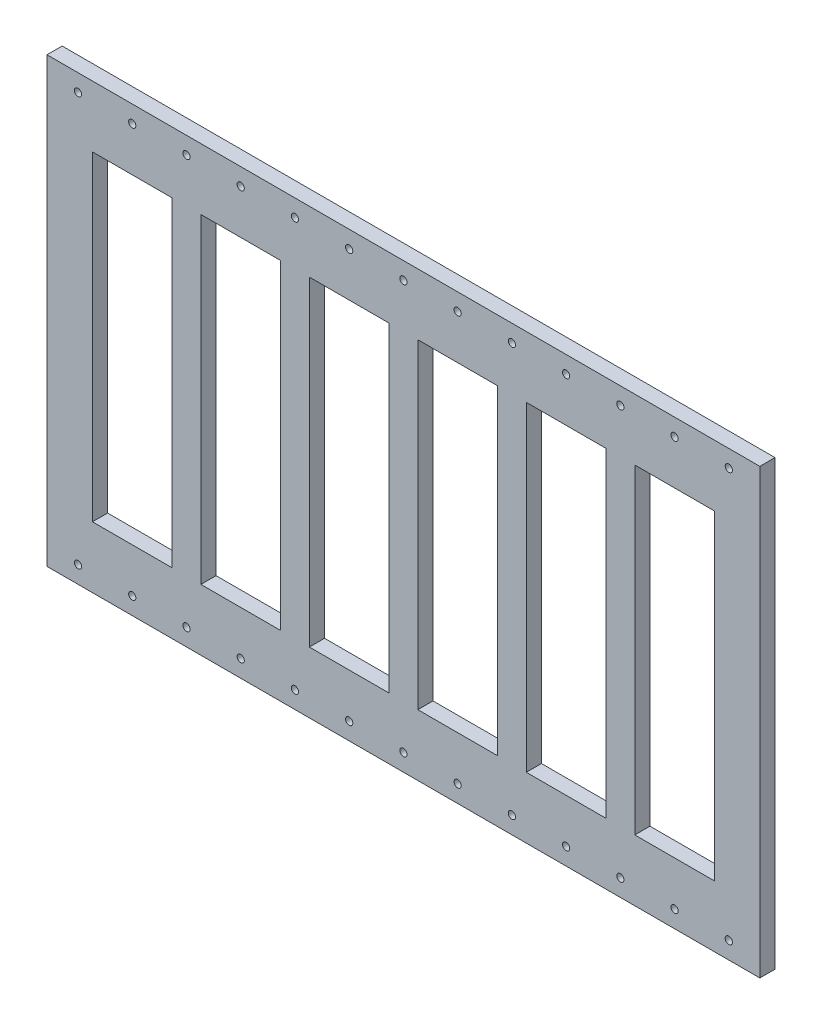
SolidWorks part; units mm, degrees
ref_plane "Front Plane" through (0, 0, 0) normal (0, 0, 1) x (1, 0, 0)
ref_plane "Top Plane" through (0, 0, 0) normal (0, 1, 0) x (1, 0, 0)
ref_plane "Right Plane" through (0, 0, 0) normal (1, 0, 0) x (0, 0, -1)
sketch "Sketch1" plane through (0, 0, 0) normal (0, 0, 1) x (1, 0, 0)
  line L0 (34.25, 211.186) -> (34.25, 251.5) construction
  line L1 (0, 0) -> (428.0041, 0) construction
  line L2 (0, 0) -> (0, 211.186) construction
  line L3 (0, 211.186) -> (428.0041, 211.186) construction
  line L4 (428.0041, 0) -> (428.0041, 211.186) construction
  line L5 (-21.95, -40.454) -> (447.95, -40.454)
  line L6 (0, 211.186) -> (0, 0) construction
  line L7 (105.75, 211.186) -> (105.75, 251.5) construction
  line L8 (8, 211.186) -> (8, 0) construction
  line L9 (447.95, -40.454) -> (447.95, 251.64)
  line L10 (60.5, 211.186) -> (60.5, 0) construction
  line L11 (177.25, 211.186) -> (177.25, 251.5) construction
  line L12 (79.5, 211.186) -> (79.5, 0) construction
  line L13 (8, 211.186) -> (60.5, 211.186)
  line L14 (428.0041, 211.186) -> (428.0041, 0) construction
  line L15 (8, 211.186) -> (8, 0)
  line L16 (418, 211.186) -> (418, 0) construction
  line L17 (132, 211.186) -> (132, 0) construction
  line L18 (8, 0) -> (60.5, 0)
  line L19 (151, 211.186) -> (151, 0) construction
  line L20 (60.5, 211.186) -> (60.5, 0)
  line L21 (203.5, 211.186) -> (203.5, 0) construction
  line L22 (79.5, 0) -> (132, 0)
  line L23 (222.5, 211.186) -> (222.5, 0) construction
  line L24 (79.5, 0) -> (79.5, 211.186)
  line L25 (275, 211.186) -> (275, 0) construction
  line L26 (79.5, 211.186) -> (132, 211.186)
  line L27 (294, 211.186) -> (294, 0) construction
  line L28 (132, 0) -> (132, 211.186)
  line L29 (346.5, 211.186) -> (346.5, 0) construction
  line L30 (151, 211.186) -> (203.5, 211.186)
  line L31 (365.5, 211.186) -> (365.5, 0) construction
  line L32 (151, 211.186) -> (151, 0)
  line L33 (0, 0) -> (428.0041, 0) construction
  line L34 (0, 0) -> (0, -40) construction
  line L35 (0, -40) -> (428.0041, -40) construction
  line L36 (428.0041, 0) -> (428.0041, -40) construction
  line L37 (0, 211.186) -> (428.0041, 211.186) construction
  line L38 (0, 211.186) -> (0, 251.5) construction
  line L39 (0, 251.5) -> (428.0041, 251.5) construction
  line L40 (428.0041, 211.186) -> (428.0041, 251.5) construction
  line L41 (151, 0) -> (203.5, 0)
  line L42 (203.5, 211.186) -> (203.5, 0)
  line L43 (222.5, 0) -> (275, 0)
  line L44 (222.5, 0) -> (222.5, 211.186)
  line L45 (222.5, 211.186) -> (275, 211.186)
  line L46 (275, 0) -> (275, 211.186)
  line L47 (294, 211.186) -> (346.5, 211.186)
  line L48 (294, 211.186) -> (294, 0)
  line L49 (294, 0) -> (346.5, 0)
  line L50 (346.5, 211.186) -> (346.5, 0)
  line L51 (365.5, 0) -> (418, 0)
  line L52 (365.5, 0) -> (365.5, 211.186)
  line L53 (365.5, 211.186) -> (418, 211.186)
  line L54 (418, 0) -> (418, 211.186)
  line L55 (-21.95, -40.454) -> (-21.95, 251.64)
  line L56 (248.75, 211.186) -> (248.75, 251.5) construction
  line L57 (320.25, 211.186) -> (320.25, 251.5) construction
  line L58 (391.75, 211.186) -> (391.75, 251.5) construction
  line L59 (-21.95, 251.64) -> (447.95, 251.64)
  line L60 (-21.95, 240.3665) -> (428.0041, 240.3665) construction
  line L61 (-21.95, -29.1805) -> (428.0041, -29.1805) construction
  line L62 (34.25, 0) -> (34.25, -40) construction
  line L63 (320.25, 0) -> (320.25, -40) construction
  line L64 (105.75, 0) -> (105.75, -40) construction
  line L65 (391.75, 0) -> (391.75, -40) construction
  line L66 (177.25, 0) -> (177.25, -40) construction
  line L67 (89.1985, 211.186) -> (89.1985, 251.64) construction
  line L68 (248.75, 0) -> (248.75, -40) construction
  line L69 (89.1985, 0) -> (89.1985, -40.454) construction
  line L70 (158.3258, 251.64) -> (158.3258, 240.3665) construction
  line L71 (158.3258, -40.454) -> (158.3258, -29.1805) construction
  line L72 (-1.5, 251.64) -> (-1.5, -40.454) construction
  line L73 (8, 65.3972) -> (-21.95, 65.3972) construction
  circle A0 centre (34.25, -29.1805) radius 2.3812
  circle A1 centre (70, -29.1805) radius 2.3813
  circle A2 centre (105.75, -29.1805) radius 2.3813
  circle A3 centre (141.5, -29.1805) radius 2.3813
  circle A4 centre (177.25, -29.1805) radius 2.3813
  circle A5 centre (213, -29.1805) radius 2.3813
  circle A6 centre (248.75, -29.1805) radius 2.3813
  circle A7 centre (284.5, -29.1805) radius 2.3813
  circle A8 centre (320.25, -29.1805) radius 2.3813
  circle A9 centre (356, -29.1805) radius 2.3813
  circle A10 centre (391.75, -29.1805) radius 2.3813
  circle A11 centre (427.5, -29.1805) radius 2.3813
  circle A12 centre (-1.5, 240.3665) radius 2.3812
  circle A14 centre (34.25, 240.3665) radius 2.3812
  circle A16 centre (70, 240.3665) radius 2.3813
  circle A18 centre (105.75, 240.3665) radius 2.3813
  circle A20 centre (141.5, 240.3665) radius 2.3813
  circle A22 centre (177.25, 240.3665) radius 2.3813
  circle A23 centre (213, 240.3665) radius 2.3813
  circle A24 centre (-1.5, -29.1805) radius 2.3813
  circle A25 centre (248.75, 240.3665) radius 2.3812
  circle A26 centre (284.5, 240.3665) radius 2.3813
  circle A27 centre (320.25, 240.3665) radius 2.3813
  circle A28 centre (356, 240.3665) radius 2.3813
  circle A29 centre (391.75, 240.3665) radius 2.3813
  circle A30 centre (427.5, 240.3665) radius 2.3813
  dimension "D2" = 13
  dimension "D1" = 5
  dimension "D3" = 13
extrude "Boss-Extrude1" add sketch "Sketch1" along normal blind 10
sketch "Sketch4" plane through (0, 0, 10) normal (0, 0, -1) x (-1, 0, 0)
  line L0 (-391.75, 251.64) -> (-391.75, -40.454) construction
  line L1 (-447.95, 184.344) -> (21.95, 184.344) construction
  line L2 (-320.25, 251.64) -> (-320.25, -40.454) construction
  line L3 (21.95, 26.844) -> (-447.95, 26.844) construction
  line L4 (-248.75, 251.64) -> (-248.75, -40.454) construction
  line L5 (-177.25, 251.64) -> (-177.25, -40.454) construction
  line L6 (-105.75, 251.64) -> (-105.75, -40.454) construction
  line L7 (-34.25, 251.64) -> (-34.25, -40.454) construction
  line L8 (-447.95, 131.844) -> (21.95, 131.844) construction
  line L10 (21.95, 79.344) -> (-447.95, 79.344) construction
  line L11 (21.95, -40.454) -> (-447.95, -40.454) construction
  line L12 (-447.95, 251.64) -> (21.95, 251.64) construction
  line L13 (21.95, 251.64) -> (21.95, -40.454) construction
  line L14 (-447.95, -40.454) -> (-447.95, 251.64) construction
  circle A0 centre (-391.75, 26.844) radius 1.5
  circle A1 centre (-320.25, 26.844) radius 1.5
  circle A2 centre (-248.75, 26.844) radius 1.5
  circle A3 centre (-177.25, 26.844) radius 1.5
  circle A4 centre (-105.75, 26.844) radius 1.5
  circle A5 centre (-34.25, 26.844) radius 1.5
  circle A6 centre (-320.25, 79.344) radius 1.5
  circle A7 centre (-248.75, 79.344) radius 1.5
  circle A8 centre (-177.25, 79.344) radius 1.5
  circle A9 centre (-105.75, 79.344) radius 1.5
  circle A10 centre (-34.25, 79.344) radius 1.5
  circle A11 centre (-320.25, 131.844) radius 1.5
  circle A12 centre (-248.75, 131.844) radius 1.5
  circle A13 centre (-177.25, 131.844) radius 1.5
  circle A14 centre (-105.75, 131.844) radius 1.5
  circle A15 centre (-34.25, 131.844) radius 1.5
  circle A16 centre (-320.25, 184.344) radius 1.5
  circle A17 centre (-248.75, 184.344) radius 1.5
  circle A18 centre (-177.25, 184.344) radius 1.5
  circle A19 centre (-105.75, 184.344) radius 1.5
  circle A20 centre (-34.25, 184.344) radius 1.5
  circle A21 centre (-391.75, 79.344) radius 1.5
  circle A22 centre (-391.75, 131.844) radius 1.5
  circle A23 centre (-391.75, 184.344) radius 1.5
  dimension "D2" = 6
  dimension "D1" = 6
  dimension "D3" = 4
